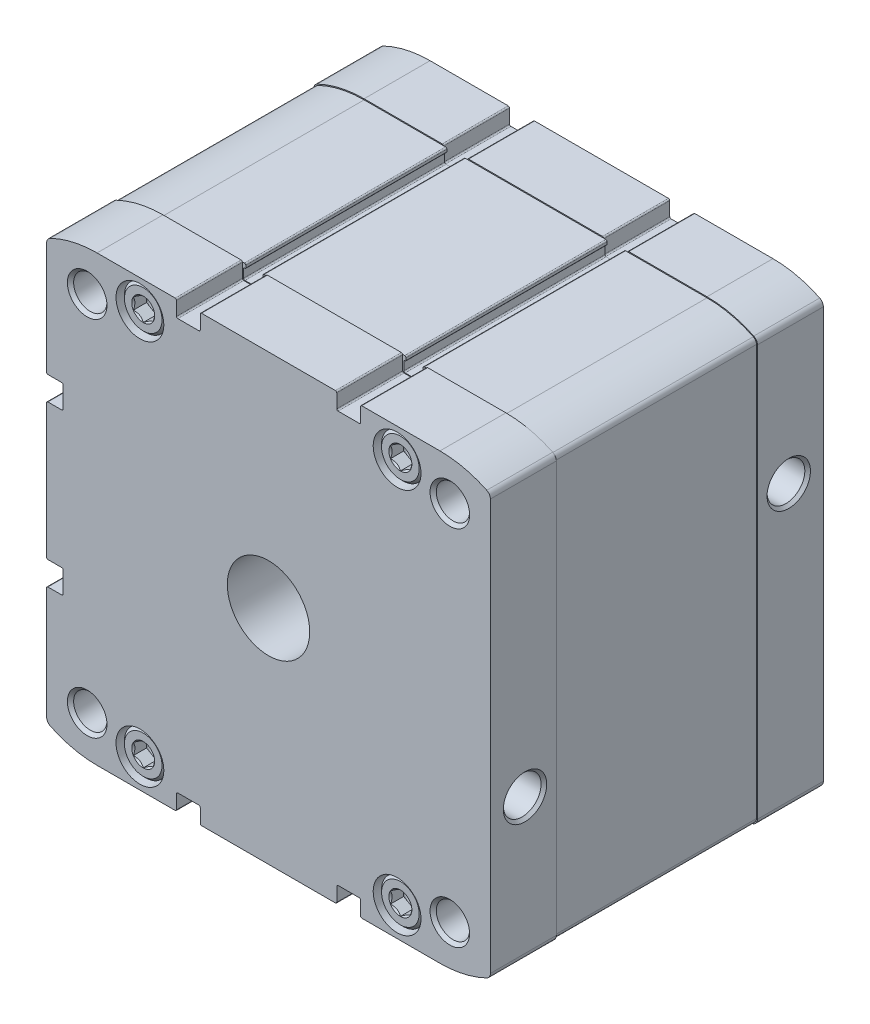
SolidWorks part; units mm, degrees
ref_plane "Front Plane" through (0, 0, 0) normal (0, 0, 1) x (1, 0, 0)
ref_plane "Top Plane" through (0, 0, 0) normal (0, 1, 0) x (1, 0, 0)
ref_plane "Right Plane" through (0, 0, 0) normal (1, 0, 0) x (0, 0, -1)
ref_plane "Plane1" through (0, 0, 0) normal (0, 0, 1) x (1, 0, 0)
sketch "Sketch1" plane through (0, 0, 0) normal (0, 0, 1) x (1, 0, 0)
  line L0 (-66.9, 27.9) -> (-62.7, 27.9)
  line L1 (-62.3, 27.5) -> (-62.3, 21.1)
  line L2 (-62.7, 20.7) -> (-66.9, 20.7)
  line L3 (-67.3, 20.3) -> (-67.3, -20.3)
  line L4 (-66.9, -20.7) -> (-62.7, -20.7)
  line L5 (-62.3, -21.1) -> (-62.3, -27.5)
  line L6 (-62.7, -27.9) -> (-66.9, -27.9)
  line L7 (-67.3, -28.3) -> (-67.3, -62.3009)
  line L8 (-52, -67.3) -> (-28.3, -67.3)
  line L9 (-27.9, -66.9) -> (-27.9, -62.7)
  line L10 (-27.5, -62.3) -> (-21.1, -62.3)
  line L11 (-20.7, -62.7) -> (-20.7, -66.9)
  line L12 (-20.3, -67.3) -> (20.3, -67.3)
  line L13 (20.7, -66.9) -> (20.7, -62.7)
  line L14 (21.1, -62.3) -> (27.5, -62.3)
  line L15 (27.9, -62.7) -> (27.9, -66.9)
  line L16 (28.3, -67.3) -> (52, -67.3)
  line L17 (67.3, -62.3009) -> (67.3, 62.3009)
  line L18 (52, 67.3) -> (28.3, 67.3)
  line L19 (27.9, 66.9) -> (27.9, 62.7)
  line L20 (27.5, 62.3) -> (21.1, 62.3)
  line L21 (20.7, 62.7) -> (20.7, 66.9)
  line L22 (20.3, 67.3) -> (-20.3, 67.3)
  line L23 (-20.7, 66.9) -> (-20.7, 62.7)
  line L24 (-21.1, 62.3) -> (-27.5, 62.3)
  line L25 (-27.9, 62.7) -> (-27.9, 66.9)
  line L26 (-28.3, 67.3) -> (-52, 67.3)
  line L27 (-67.3, 62.3009) -> (-67.3, 28.3)
  arc A0 (-67.3, 28.3) -> (-66.9, 27.9) centre (-66.9, 28.3) ccw
  arc A1 (-62.7, 27.9) -> (-62.3, 27.5) centre (-62.7, 27.5) cw
  arc A2 (-62.3, 21.1) -> (-62.7, 20.7) centre (-62.7, 21.1) cw
  arc A3 (-66.9, 20.7) -> (-67.3, 20.3) centre (-66.9, 20.3) ccw
  arc A4 (-67.3, -20.3) -> (-66.9, -20.7) centre (-66.9, -20.3) ccw
  arc A5 (-62.7, -20.7) -> (-62.3, -21.1) centre (-62.7, -21.1) cw
  arc A6 (-62.3, -27.5) -> (-62.7, -27.9) centre (-62.7, -27.5) cw
  arc A7 (-66.9, -27.9) -> (-67.3, -28.3) centre (-66.9, -28.3) ccw
  arc A8 (-67.3, -62.3009) -> (-66.1966, -64.0575) centre (-65.35, -62.3009) ccw
  arc A9 (-66.1966, -64.0575) -> (-52, -67.3) centre (-52, -34.6) ccw
  arc A10 (-28.3, -67.3) -> (-27.9, -66.9) centre (-28.3, -66.9) ccw
  arc A11 (-27.9, -62.7) -> (-27.5, -62.3) centre (-27.5, -62.7) cw
  arc A12 (-21.1, -62.3) -> (-20.7, -62.7) centre (-21.1, -62.7) cw
  arc A13 (-20.7, -66.9) -> (-20.3, -67.3) centre (-20.3, -66.9) ccw
  arc A14 (20.3, -67.3) -> (20.7, -66.9) centre (20.3, -66.9) ccw
  arc A15 (20.7, -62.7) -> (21.1, -62.3) centre (21.1, -62.7) cw
  arc A16 (27.5, -62.3) -> (27.9, -62.7) centre (27.5, -62.7) cw
  arc A17 (27.9, -66.9) -> (28.3, -67.3) centre (28.3, -66.9) ccw
  arc A18 (52, -67.3) -> (66.1966, -64.0575) centre (52, -34.6) ccw
  arc A19 (66.1966, -64.0575) -> (67.3, -62.3009) centre (65.35, -62.3009) ccw
  arc A20 (67.3, 62.3009) -> (66.1966, 64.0575) centre (65.35, 62.3009) ccw
  arc A21 (66.1966, 64.0575) -> (52, 67.3) centre (52, 34.6) ccw
  arc A22 (28.3, 67.3) -> (27.9, 66.9) centre (28.3, 66.9) ccw
  arc A23 (27.9, 62.7) -> (27.5, 62.3) centre (27.5, 62.7) cw
  arc A24 (21.1, 62.3) -> (20.7, 62.7) centre (21.1, 62.7) cw
  arc A25 (20.7, 66.9) -> (20.3, 67.3) centre (20.3, 66.9) ccw
  arc A26 (-20.3, 67.3) -> (-20.7, 66.9) centre (-20.3, 66.9) ccw
  arc A27 (-20.7, 62.7) -> (-21.1, 62.3) centre (-21.1, 62.7) cw
  arc A28 (-27.5, 62.3) -> (-27.9, 62.7) centre (-27.5, 62.7) cw
  arc A29 (-27.9, 66.9) -> (-28.3, 67.3) centre (-28.3, 66.9) ccw
  arc A30 (-52, 67.3) -> (-66.1966, 64.0575) centre (-52, 34.6) ccw
  arc A31 (-66.1966, 64.0575) -> (-67.3, 62.3009) centre (-65.35, 62.3009) ccw
extrude "Boss-Extrude1" add sketch "Sketch1" against normal blind 101
ref_plane "Plane2" through (0, 0, -20) normal (0, 0, 1) x (1, 0, 0)
sketch "Sketch2" plane through (0, 0, -20) normal (0, 0, 1) x (1, 0, 0)
  line L0 (-67, 67) -> (-67, -67)
  line L1 (-67, -67) -> (67, -67)
  line L2 (67, -67) -> (67, 67)
  line L3 (67, 67) -> (-67, 67)
extrude "Boss-Extrude2" add sketch "Sketch2" against normal blind 61
ref_plane "Plane3" through (0, 0, -20) normal (0, 0, 1) x (1, 0, 0)
sketch "Sketch3" plane through (0, 0, -20) normal (0, 0, 1) x (1, 0, 0)
  line L0 (-100, 100) -> (-100, -100)
  line L1 (-100, -100) -> (100, -100)
  line L2 (100, -100) -> (100, 100)
  line L3 (100, 100) -> (-100, 100)
  line L4 (-66.6, 26.9) -> (-65.9, 26.9)
  line L5 (-65.7, 27.1) -> (-65.7, 27.35)
  line L6 (-65.5, 27.55) -> (-62.9, 27.55)
  line L7 (-62.5, 27.15) -> (-62.5, 21.45)
  line L8 (-62.9, 21.05) -> (-65.5, 21.05)
  line L9 (-65.7, 21.25) -> (-65.7, 21.5)
  line L10 (-65.9, 21.7) -> (-66.6, 21.7)
  line L11 (-67, 21.3) -> (-67, -21.3)
  line L12 (-66.6, -21.7) -> (-65.9, -21.7)
  line L13 (-65.7, -21.5) -> (-65.7, -21.25)
  line L14 (-65.5, -21.05) -> (-62.9, -21.05)
  line L15 (-62.5, -21.45) -> (-62.5, -27.15)
  line L16 (-62.9, -27.55) -> (-65.5, -27.55)
  line L17 (-65.7, -27.35) -> (-65.7, -27.1)
  line L18 (-65.9, -26.9) -> (-66.6, -26.9)
  line L19 (-67, -27.3) -> (-67, -62.2695)
  line L20 (-52, -67) -> (-27.3, -67)
  line L21 (-26.9, -66.6) -> (-26.9, -65.9)
  line L22 (-27.1, -65.7) -> (-27.35, -65.7)
  line L23 (-27.55, -65.5) -> (-27.55, -62.9)
  line L24 (-27.15, -62.5) -> (-21.45, -62.5)
  line L25 (-21.05, -62.9) -> (-21.05, -65.5)
  line L26 (-21.25, -65.7) -> (-21.5, -65.7)
  line L27 (-21.7, -65.9) -> (-21.7, -66.6)
  line L28 (-21.3, -67) -> (21.3, -67)
  line L29 (21.7, -66.6) -> (21.7, -65.9)
  line L30 (21.5, -65.7) -> (21.25, -65.7)
  line L31 (21.05, -65.5) -> (21.05, -62.9)
  line L32 (21.45, -62.5) -> (27.15, -62.5)
  line L33 (27.55, -62.9) -> (27.55, -65.5)
  line L34 (27.35, -65.7) -> (27.1, -65.7)
  line L35 (26.9, -65.9) -> (26.9, -66.6)
  line L36 (27.3, -67) -> (52, -67)
  line L37 (67, -62.2695) -> (67, 62.2695)
  line L38 (52, 67) -> (27.3, 67)
  line L39 (26.9, 66.6) -> (26.9, 65.9)
  line L40 (27.1, 65.7) -> (27.35, 65.7)
  line L41 (27.55, 65.5) -> (27.55, 62.9)
  line L42 (27.15, 62.5) -> (21.45, 62.5)
  line L43 (21.05, 62.9) -> (21.05, 65.5)
  line L44 (21.25, 65.7) -> (21.5, 65.7)
  line L45 (21.7, 65.9) -> (21.7, 66.6)
  line L46 (21.3, 67) -> (-21.3, 67)
  line L47 (-21.7, 66.6) -> (-21.7, 65.9)
  line L48 (-21.5, 65.7) -> (-21.25, 65.7)
  line L49 (-21.05, 65.5) -> (-21.05, 62.9)
  line L50 (-21.45, 62.5) -> (-27.15, 62.5)
  line L51 (-27.55, 62.9) -> (-27.55, 65.5)
  line L52 (-27.35, 65.7) -> (-27.1, 65.7)
  line L53 (-26.9, 65.9) -> (-26.9, 66.6)
  line L54 (-27.3, 67) -> (-52, 67)
  line L55 (-67, 62.2695) -> (-67, 27.3)
  arc A0 (-67, 27.3) -> (-66.6, 26.9) centre (-66.6, 27.3) ccw
  arc A1 (-65.9, 26.9) -> (-65.7, 27.1) centre (-65.9, 27.1) ccw
  arc A2 (-65.7, 27.35) -> (-65.5, 27.55) centre (-65.5, 27.35) cw
  arc A3 (-62.9, 27.55) -> (-62.5, 27.15) centre (-62.9, 27.15) cw
  arc A4 (-62.5, 21.45) -> (-62.9, 21.05) centre (-62.9, 21.45) cw
  arc A5 (-65.5, 21.05) -> (-65.7, 21.25) centre (-65.5, 21.25) cw
  arc A6 (-65.7, 21.5) -> (-65.9, 21.7) centre (-65.9, 21.5) ccw
  arc A7 (-66.6, 21.7) -> (-67, 21.3) centre (-66.6, 21.3) ccw
  arc A8 (-67, -21.3) -> (-66.6, -21.7) centre (-66.6, -21.3) ccw
  arc A9 (-65.9, -21.7) -> (-65.7, -21.5) centre (-65.9, -21.5) ccw
  arc A10 (-65.7, -21.25) -> (-65.5, -21.05) centre (-65.5, -21.25) cw
  arc A11 (-62.9, -21.05) -> (-62.5, -21.45) centre (-62.9, -21.45) cw
  arc A12 (-62.5, -27.15) -> (-62.9, -27.55) centre (-62.9, -27.15) cw
  arc A13 (-65.5, -27.55) -> (-65.7, -27.35) centre (-65.5, -27.35) cw
  arc A14 (-65.7, -27.1) -> (-65.9, -26.9) centre (-65.9, -27.1) ccw
  arc A15 (-66.6, -26.9) -> (-67, -27.3) centre (-66.6, -27.3) ccw
  arc A16 (-67, -62.2695) -> (-66.0365, -63.8017) centre (-65.3, -62.2695) ccw
  arc A17 (-66.0365, -63.8017) -> (-52, -67) centre (-52, -34.6) ccw
  arc A18 (-27.3, -67) -> (-26.9, -66.6) centre (-27.3, -66.6) ccw
  arc A19 (-26.9, -65.9) -> (-27.1, -65.7) centre (-27.1, -65.9) ccw
  arc A20 (-27.35, -65.7) -> (-27.55, -65.5) centre (-27.35, -65.5) cw
  arc A21 (-27.55, -62.9) -> (-27.15, -62.5) centre (-27.15, -62.9) cw
  arc A22 (-21.45, -62.5) -> (-21.05, -62.9) centre (-21.45, -62.9) cw
  arc A23 (-21.05, -65.5) -> (-21.25, -65.7) centre (-21.25, -65.5) cw
  arc A24 (-21.5, -65.7) -> (-21.7, -65.9) centre (-21.5, -65.9) ccw
  arc A25 (-21.7, -66.6) -> (-21.3, -67) centre (-21.3, -66.6) ccw
  arc A26 (21.3, -67) -> (21.7, -66.6) centre (21.3, -66.6) ccw
  arc A27 (21.7, -65.9) -> (21.5, -65.7) centre (21.5, -65.9) ccw
  arc A28 (21.25, -65.7) -> (21.05, -65.5) centre (21.25, -65.5) cw
  arc A29 (21.05, -62.9) -> (21.45, -62.5) centre (21.45, -62.9) cw
  arc A30 (27.15, -62.5) -> (27.55, -62.9) centre (27.15, -62.9) cw
  arc A31 (27.55, -65.5) -> (27.35, -65.7) centre (27.35, -65.5) cw
  arc A32 (27.1, -65.7) -> (26.9, -65.9) centre (27.1, -65.9) ccw
  arc A33 (26.9, -66.6) -> (27.3, -67) centre (27.3, -66.6) ccw
  arc A34 (52, -67) -> (66.0365, -63.8017) centre (52, -34.6) ccw
  arc A35 (66.0365, -63.8017) -> (67, -62.2695) centre (65.3, -62.2695) ccw
  arc A36 (67, 62.2695) -> (66.0365, 63.8017) centre (65.3, 62.2695) ccw
  arc A37 (66.0365, 63.8017) -> (52, 67) centre (52, 34.6) ccw
  arc A38 (27.3, 67) -> (26.9, 66.6) centre (27.3, 66.6) ccw
  arc A39 (26.9, 65.9) -> (27.1, 65.7) centre (27.1, 65.9) ccw
  arc A40 (27.35, 65.7) -> (27.55, 65.5) centre (27.35, 65.5) cw
  arc A41 (27.55, 62.9) -> (27.15, 62.5) centre (27.15, 62.9) cw
  arc A42 (21.45, 62.5) -> (21.05, 62.9) centre (21.45, 62.9) cw
  arc A43 (21.05, 65.5) -> (21.25, 65.7) centre (21.25, 65.5) cw
  arc A44 (21.5, 65.7) -> (21.7, 65.9) centre (21.5, 65.9) ccw
  arc A45 (21.7, 66.6) -> (21.3, 67) centre (21.3, 66.6) ccw
  arc A46 (-21.3, 67) -> (-21.7, 66.6) centre (-21.3, 66.6) ccw
  arc A47 (-21.7, 65.9) -> (-21.5, 65.7) centre (-21.5, 65.9) ccw
  arc A48 (-21.25, 65.7) -> (-21.05, 65.5) centre (-21.25, 65.5) cw
  arc A49 (-21.05, 62.9) -> (-21.45, 62.5) centre (-21.45, 62.9) cw
  arc A50 (-27.15, 62.5) -> (-27.55, 62.9) centre (-27.15, 62.9) cw
  arc A51 (-27.55, 65.5) -> (-27.35, 65.7) centre (-27.35, 65.5) cw
  arc A52 (-27.1, 65.7) -> (-26.9, 65.9) centre (-27.1, 65.9) ccw
  arc A53 (-26.9, 66.6) -> (-27.3, 67) centre (-27.3, 66.6) ccw
  arc A54 (-52, 67) -> (-66.0365, 63.8017) centre (-52, 34.6) ccw
  arc A55 (-66.0365, 63.8017) -> (-67, 62.2695) centre (-65.3, 62.2695) ccw
extrude "Cut-Extrude1" cut sketch "Sketch3" against normal blind 61
ref_plane "Plane4" through (0, -21.15, 0) normal (0, 1, 0) x (1, 0, 0)
sketch "Sketch4" plane through (0, -21.15, 0) normal (0, 1, 0) x (1, 0, 0)
  line L0 (39.5, 10.5) -> (39.5, 16.2225)
  line L1 (39.5, 16.2225) -> (66.444, 16.2225)
  line L2 (66.444, 16.2225) -> (67.3, 17.0785)
  line L3 (67.3, 17.0785) -> (67.3, 10.5)
  line L4 (67.3, 10.5) -> (39.5, 10.5)
  line L5 (67.3, 10.5) -> (39.5, 10.5) construction
revolve "Cut-Revolve1" cut sketch "Sketch4" angle 360 about L5
cosmetic thread "Cosmetic Thread1" parameters "D1"=13, "D2"=13.157
ref_plane "Plane5" through (0, 21.15, 0) normal (0, 1, 0) x (1, 0, 0)
sketch "Sketch5" plane through (0, 21.15, 0) normal (0, 1, 0) x (1, 0, 0)
  line L0 (39.5, 90.5) -> (39.5, 96.2225)
  line L1 (39.5, 96.2225) -> (66.444, 96.2225)
  line L2 (66.444, 96.2225) -> (67.3, 97.0785)
  line L3 (67.3, 97.0785) -> (67.3, 90.5)
  line L4 (67.3, 90.5) -> (39.5, 90.5)
  line L5 (67.3, 90.5) -> (39.5, 90.5) construction
revolve "Cut-Revolve2" cut sketch "Sketch5" angle 360 about L5
cosmetic thread "Cosmetic Thread2" parameters "D1"=13, "D2"=13.157
ref_plane "Plane6" through (0, 0, 0) normal (1, 0, 0) x (0, 0, -1)
sketch "Sketch6" plane through (0, 0, 0) normal (1, 0, 0) x (0, 0, -1)
  line L0 (-1, 0) -> (-1, 12.5)
  line L1 (-1, 12.5) -> (28.75, 12.5)
  line L2 (28.75, 12.5) -> (28.75, 62.5)
  line L3 (28.75, 62.5) -> (80, 62.5)
  line L4 (80, 62.5) -> (80, 0)
  line L5 (80, 0) -> (-1, 0)
  line L6 (80, 0) -> (-1, 0) construction
revolve "Cut-Revolve3" cut sketch "Sketch6" angle 360 about L6
ref_plane "Plane7" through (0, 0, 0) normal (1, 0, 0) x (0, 0, -1)
sketch "Sketch7" plane through (0, 0, 0) normal (1, 0, 0) x (0, 0, -1)
  line L0 (98.4, 0) -> (98.4, 6)
  line L1 (98.4, 6) -> (101, 6)
  line L2 (101, 6) -> (101, 0)
  line L3 (101, 0) -> (98.4, 0)
  line L4 (101, 0) -> (98.4, 0) construction
revolve "Cut-Revolve4" cut sketch "Sketch7" angle 360 about L4
ref_plane "Plane8" through (0, 58.5, 0) normal (0, 1, 0) x (1, 0, 0)
sketch "Sketch8" plane through (0, 58.5, 0) normal (0, 1, 0) x (1, 0, 0)
  line L0 (39, 5.8038) -> (42, 5)
  line L1 (42, 5) -> (42, 1.48)
  line L2 (42, 1.48) -> (42.48, 1)
  line L3 (42.48, 1) -> (44.7, 1)
  line L4 (44.7, 1) -> (45.5, 1.8)
  line L5 (45.5, 1.8) -> (45.5, 9)
  line L6 (45.5, 9) -> (46.25, 9)
  line L7 (46.25, 9) -> (46.25, -1)
  line L8 (46.25, -1) -> (39, -1)
  line L9 (39, -1) -> (39, 5.8038)
  line L10 (39, -1) -> (39, 5.8038) construction
revolve "Cut-Revolve5" cut sketch "Sketch8" angle 360 about L10
ref_plane "Plane9" through (0, 58.5, 0) normal (0, 1, 0) x (1, 0, 0)
sketch "Sketch9" plane through (0, 58.5, 0) normal (0, 1, 0) x (1, 0, 0)
  line L0 (-39, 5.8038) -> (-36, 5)
  line L1 (-36, 5) -> (-36, 1.48)
  line L2 (-36, 1.48) -> (-35.52, 1)
  line L3 (-35.52, 1) -> (-33.3, 1)
  line L4 (-33.3, 1) -> (-32.5, 1.8)
  line L5 (-32.5, 1.8) -> (-32.5, 9)
  line L6 (-32.5, 9) -> (-31.75, 9)
  line L7 (-31.75, 9) -> (-31.75, -1)
  line L8 (-31.75, -1) -> (-39, -1)
  line L9 (-39, -1) -> (-39, 5.8038)
  line L10 (-39, -1) -> (-39, 5.8038) construction
revolve "Cut-Revolve6" cut sketch "Sketch9" angle 360 about L10
ref_plane "Plane10" through (0, -58.5, 0) normal (0, 1, 0) x (1, 0, 0)
sketch "Sketch10" plane through (0, -58.5, 0) normal (0, 1, 0) x (1, 0, 0)
  line L0 (39, 5.8038) -> (42, 5)
  line L1 (42, 5) -> (42, 1.48)
  line L2 (42, 1.48) -> (42.48, 1)
  line L3 (42.48, 1) -> (44.7, 1)
  line L4 (44.7, 1) -> (45.5, 1.8)
  line L5 (45.5, 1.8) -> (45.5, 9)
  line L6 (45.5, 9) -> (46.25, 9)
  line L7 (46.25, 9) -> (46.25, -1)
  line L8 (46.25, -1) -> (39, -1)
  line L9 (39, -1) -> (39, 5.8038)
  line L10 (39, -1) -> (39, 5.8038) construction
revolve "Cut-Revolve7" cut sketch "Sketch10" angle 360 about L10
ref_plane "Plane11" through (0, -58.5, 0) normal (0, 1, 0) x (1, 0, 0)
sketch "Sketch11" plane through (0, -58.5, 0) normal (0, 1, 0) x (1, 0, 0)
  line L0 (-39, 5.8038) -> (-36, 5)
  line L1 (-36, 5) -> (-36, 1.48)
  line L2 (-36, 1.48) -> (-35.52, 1)
  line L3 (-35.52, 1) -> (-33.3, 1)
  line L4 (-33.3, 1) -> (-32.5, 1.8)
  line L5 (-32.5, 1.8) -> (-32.5, 9)
  line L6 (-32.5, 9) -> (-31.75, 9)
  line L7 (-31.75, 9) -> (-31.75, -1)
  line L8 (-31.75, -1) -> (-39, -1)
  line L9 (-39, -1) -> (-39, 5.8038)
  line L10 (-39, -1) -> (-39, 5.8038) construction
revolve "Cut-Revolve8" cut sketch "Sketch11" angle 360 about L10
ref_plane "Plane12" through (0, 58.5, 0) normal (0, 1, 0) x (1, 0, 0)
sketch "Sketch12" plane through (0, 58.5, 0) normal (0, 1, 0) x (1, 0, 0)
  line L0 (39, 102) -> (46.25, 102)
  line L1 (46.25, 102) -> (46.25, 92)
  line L2 (46.25, 92) -> (45.5, 92)
  line L3 (45.5, 92) -> (45.5, 99.2)
  line L4 (45.5, 99.2) -> (44.7, 100)
  line L5 (44.7, 100) -> (42.48, 100)
  line L6 (42.48, 100) -> (42, 99.52)
  line L7 (42, 99.52) -> (42, 96)
  line L8 (42, 96) -> (39, 95.1962)
  line L9 (39, 95.1962) -> (39, 102)
  line L10 (39, 95.1962) -> (39, 102) construction
revolve "Cut-Revolve9" cut sketch "Sketch12" angle 360 about L10
ref_plane "Plane13" through (0, 58.5, 0) normal (0, 1, 0) x (1, 0, 0)
sketch "Sketch13" plane through (0, 58.5, 0) normal (0, 1, 0) x (1, 0, 0)
  line L0 (-39, 102) -> (-31.75, 102)
  line L1 (-31.75, 102) -> (-31.75, 92)
  line L2 (-31.75, 92) -> (-32.5, 92)
  line L3 (-32.5, 92) -> (-32.5, 99.2)
  line L4 (-32.5, 99.2) -> (-33.3, 100)
  line L5 (-33.3, 100) -> (-35.52, 100)
  line L6 (-35.52, 100) -> (-36, 99.52)
  line L7 (-36, 99.52) -> (-36, 96)
  line L8 (-36, 96) -> (-39, 95.1962)
  line L9 (-39, 95.1962) -> (-39, 102)
  line L10 (-39, 95.1962) -> (-39, 102) construction
revolve "Cut-Revolve10" cut sketch "Sketch13" angle 360 about L10
ref_plane "Plane14" through (0, -58.5, 0) normal (0, 1, 0) x (1, 0, 0)
sketch "Sketch14" plane through (0, -58.5, 0) normal (0, 1, 0) x (1, 0, 0)
  line L0 (-39, 102) -> (-31.75, 102)
  line L1 (-31.75, 102) -> (-31.75, 92)
  line L2 (-31.75, 92) -> (-32.5, 92)
  line L3 (-32.5, 92) -> (-32.5, 99.2)
  line L4 (-32.5, 99.2) -> (-33.3, 100)
  line L5 (-33.3, 100) -> (-35.52, 100)
  line L6 (-35.52, 100) -> (-36, 99.52)
  line L7 (-36, 99.52) -> (-36, 96)
  line L8 (-36, 96) -> (-39, 95.1962)
  line L9 (-39, 95.1962) -> (-39, 102)
  line L10 (-39, 95.1962) -> (-39, 102) construction
revolve "Cut-Revolve11" cut sketch "Sketch14" angle 360 about L10
ref_plane "Plane15" through (0, -58.5, 0) normal (0, 1, 0) x (1, 0, 0)
sketch "Sketch15" plane through (0, -58.5, 0) normal (0, 1, 0) x (1, 0, 0)
  line L0 (39, 102) -> (46.25, 102)
  line L1 (46.25, 102) -> (46.25, 92)
  line L2 (46.25, 92) -> (45.5, 92)
  line L3 (45.5, 92) -> (45.5, 99.2)
  line L4 (45.5, 99.2) -> (44.7, 100)
  line L5 (44.7, 100) -> (42.48, 100)
  line L6 (42.48, 100) -> (42, 99.52)
  line L7 (42, 99.52) -> (42, 96)
  line L8 (42, 96) -> (39, 95.1962)
  line L9 (39, 95.1962) -> (39, 102)
  line L10 (39, 95.1962) -> (39, 102) construction
revolve "Cut-Revolve12" cut sketch "Sketch15" angle 360 about L10
ref_plane "Plane16" through (0, 0, -1) normal (0, 0, 1) x (1, 0, 0)
sketch "Sketch16" plane through (0, 0, -1) normal (0, 0, 1) x (1, 0, 0)
  line L0 (36, 56.7679) -> (39, 55.0359)
  line L1 (39, 55.0359) -> (42, 56.7679)
  line L2 (42, 56.7679) -> (42, 60.2321)
  line L3 (42, 60.2321) -> (39, 61.9641)
  line L4 (39, 61.9641) -> (36, 60.2321)
  line L5 (36, 60.2321) -> (36, 56.7679)
extrude "Cut-Extrude2" cut sketch "Sketch16" against normal blind 4
ref_plane "Plane17" through (0, 0, -1) normal (0, 0, 1) x (1, 0, 0)
sketch "Sketch17" plane through (0, 0, -1) normal (0, 0, 1) x (1, 0, 0)
  line L0 (-42, 56.7679) -> (-39, 55.0359)
  line L1 (-39, 55.0359) -> (-36, 56.7679)
  line L2 (-36, 56.7679) -> (-36, 60.2321)
  line L3 (-36, 60.2321) -> (-39, 61.9641)
  line L4 (-39, 61.9641) -> (-42, 60.2321)
  line L5 (-42, 60.2321) -> (-42, 56.7679)
extrude "Cut-Extrude3" cut sketch "Sketch17" against normal blind 4
ref_plane "Plane18" through (0, 0, -1) normal (0, 0, 1) x (1, 0, 0)
sketch "Sketch18" plane through (0, 0, -1) normal (0, 0, 1) x (1, 0, 0)
  line L0 (-42, -60.2321) -> (-39, -61.9641)
  line L1 (-39, -61.9641) -> (-36, -60.2321)
  line L2 (-36, -60.2321) -> (-36, -56.7679)
  line L3 (-36, -56.7679) -> (-39, -55.0359)
  line L4 (-39, -55.0359) -> (-42, -56.7679)
  line L5 (-42, -56.7679) -> (-42, -60.2321)
extrude "Cut-Extrude4" cut sketch "Sketch18" against normal blind 4
ref_plane "Plane19" through (0, 0, -1) normal (0, 0, 1) x (1, 0, 0)
sketch "Sketch19" plane through (0, 0, -1) normal (0, 0, 1) x (1, 0, 0)
  line L0 (36, -60.2321) -> (39, -61.9641)
  line L1 (39, -61.9641) -> (42, -60.2321)
  line L2 (42, -60.2321) -> (42, -56.7679)
  line L3 (42, -56.7679) -> (39, -55.0359)
  line L4 (39, -55.0359) -> (36, -56.7679)
  line L5 (36, -56.7679) -> (36, -60.2321)
extrude "Cut-Extrude5" cut sketch "Sketch19" against normal blind 4
ref_plane "Plane20" through (0, 0, -100) normal (0, 0, 1) x (1, 0, 0)
sketch "Sketch20" plane through (0, 0, -100) normal (0, 0, 1) x (1, 0, 0)
  line L0 (36, 56.7679) -> (39, 55.0359)
  line L1 (39, 55.0359) -> (42, 56.7679)
  line L2 (42, 56.7679) -> (42, 60.2321)
  line L3 (42, 60.2321) -> (39, 61.9641)
  line L4 (39, 61.9641) -> (36, 60.2321)
  line L5 (36, 60.2321) -> (36, 56.7679)
extrude "Cut-Extrude6" cut sketch "Sketch20" along normal blind 4
ref_plane "Plane21" through (0, 0, -100) normal (0, 0, 1) x (1, 0, 0)
sketch "Sketch21" plane through (0, 0, -100) normal (0, 0, 1) x (1, 0, 0)
  line L0 (-42, 56.7679) -> (-39, 55.0359)
  line L1 (-39, 55.0359) -> (-36, 56.7679)
  line L2 (-36, 56.7679) -> (-36, 60.2321)
  line L3 (-36, 60.2321) -> (-39, 61.9641)
  line L4 (-39, 61.9641) -> (-42, 60.2321)
  line L5 (-42, 60.2321) -> (-42, 56.7679)
extrude "Cut-Extrude7" cut sketch "Sketch21" along normal blind 4
ref_plane "Plane22" through (0, 0, -100) normal (0, 0, 1) x (1, 0, 0)
sketch "Sketch22" plane through (0, 0, -100) normal (0, 0, 1) x (1, 0, 0)
  line L0 (-42, -60.2321) -> (-39, -61.9641)
  line L1 (-39, -61.9641) -> (-36, -60.2321)
  line L2 (-36, -60.2321) -> (-36, -56.7679)
  line L3 (-36, -56.7679) -> (-39, -55.0359)
  line L4 (-39, -55.0359) -> (-42, -56.7679)
  line L5 (-42, -56.7679) -> (-42, -60.2321)
extrude "Cut-Extrude8" cut sketch "Sketch22" along normal blind 4
ref_plane "Plane23" through (0, 0, -100) normal (0, 0, 1) x (1, 0, 0)
sketch "Sketch23" plane through (0, 0, -100) normal (0, 0, 1) x (1, 0, 0)
  line L0 (36, -60.2321) -> (39, -61.9641)
  line L1 (39, -61.9641) -> (42, -60.2321)
  line L2 (42, -60.2321) -> (42, -56.7679)
  line L3 (42, -56.7679) -> (39, -55.0359)
  line L4 (39, -55.0359) -> (36, -56.7679)
  line L5 (36, -56.7679) -> (36, -60.2321)
extrude "Cut-Extrude9" cut sketch "Sketch23" along normal blind 4
ref_plane "Plane24" through (55, 0, 0) normal (1, 0, 0) x (0, 0, -1)
sketch "Sketch24" plane through (55, 0, 0) normal (1, 0, 0) x (0, 0, -1)
  line L0 (0, 55) -> (0, 61)
  line L1 (0, 61) -> (0.947, 60.053)
  line L2 (0.947, 60.053) -> (20, 60.053)
  line L3 (20, 60.053) -> (20, 55)
  line L4 (20, 55) -> (0, 55)
  line L5 (20, 55) -> (0, 55) construction
revolve "Cut-Revolve13" cut sketch "Sketch24" angle 360 about L5
cosmetic thread "Cosmetic Thread3" parameters "D1"=20, "D2"=12
ref_plane "Plane25" through (-55, 0, 0) normal (1, 0, 0) x (0, 0, -1)
sketch "Sketch25" plane through (-55, 0, 0) normal (1, 0, 0) x (0, 0, -1)
  line L0 (0, 55) -> (0, 61)
  line L1 (0, 61) -> (0.947, 60.053)
  line L2 (0.947, 60.053) -> (20, 60.053)
  line L3 (20, 60.053) -> (20, 55)
  line L4 (20, 55) -> (0, 55)
  line L5 (20, 55) -> (0, 55) construction
revolve "Cut-Revolve14" cut sketch "Sketch25" angle 360 about L5
cosmetic thread "Cosmetic Thread4" parameters "D1"=20, "D2"=12
ref_plane "Plane26" through (55, 0, 0) normal (1, 0, 0) x (0, 0, -1)
sketch "Sketch26" plane through (55, 0, 0) normal (1, 0, 0) x (0, 0, -1)
  line L0 (0, -55) -> (0, -49)
  line L1 (0, -49) -> (0.947, -49.947)
  line L2 (0.947, -49.947) -> (20, -49.947)
  line L3 (20, -49.947) -> (20, -55)
  line L4 (20, -55) -> (0, -55)
  line L5 (20, -55) -> (0, -55) construction
revolve "Cut-Revolve15" cut sketch "Sketch26" angle 360 about L5
cosmetic thread "Cosmetic Thread5" parameters "D1"=20, "D2"=12
ref_plane "Plane27" through (-55, 0, 0) normal (1, 0, 0) x (0, 0, -1)
sketch "Sketch27" plane through (-55, 0, 0) normal (1, 0, 0) x (0, 0, -1)
  line L0 (0, -55) -> (0, -49)
  line L1 (0, -49) -> (0.947, -49.947)
  line L2 (0.947, -49.947) -> (20, -49.947)
  line L3 (20, -49.947) -> (20, -55)
  line L4 (20, -55) -> (0, -55)
  line L5 (20, -55) -> (0, -55) construction
revolve "Cut-Revolve16" cut sketch "Sketch27" angle 360 about L5
cosmetic thread "Cosmetic Thread6" parameters "D1"=20, "D2"=12
ref_plane "Plane28" through (55, 0, 0) normal (1, 0, 0) x (0, 0, -1)
sketch "Sketch28" plane through (55, 0, 0) normal (1, 0, 0) x (0, 0, -1)
  line L0 (81, 55) -> (81, 60.053)
  line L1 (81, 60.053) -> (100.053, 60.053)
  line L2 (100.053, 60.053) -> (101, 61)
  line L3 (101, 61) -> (101, 55)
  line L4 (101, 55) -> (81, 55)
  line L5 (101, 55) -> (81, 55) construction
revolve "Cut-Revolve17" cut sketch "Sketch28" angle 360 about L5
cosmetic thread "Cosmetic Thread7" parameters "D1"=20, "D2"=12
ref_plane "Plane29" through (55, 0, 0) normal (1, 0, 0) x (0, 0, -1)
sketch "Sketch29" plane through (55, 0, 0) normal (1, 0, 0) x (0, 0, -1)
  line L0 (20, 55) -> (20, 60.5)
  line L1 (20, 60.5) -> (81, 60.5)
  line L2 (81, 60.5) -> (81, 55)
  line L3 (81, 55) -> (20, 55)
  line L4 (81, 55) -> (20, 55) construction
revolve "Cut-Revolve18" cut sketch "Sketch29" angle 360 about L4
ref_plane "Plane30" through (-55, 0, 0) normal (1, 0, 0) x (0, 0, -1)
sketch "Sketch30" plane through (-55, 0, 0) normal (1, 0, 0) x (0, 0, -1)
  line L0 (81, 55) -> (81, 60.053)
  line L1 (81, 60.053) -> (100.053, 60.053)
  line L2 (100.053, 60.053) -> (101, 61)
  line L3 (101, 61) -> (101, 55)
  line L4 (101, 55) -> (81, 55)
  line L5 (101, 55) -> (81, 55) construction
revolve "Cut-Revolve19" cut sketch "Sketch30" angle 360 about L5
cosmetic thread "Cosmetic Thread8" parameters "D1"=20, "D2"=12
ref_plane "Plane31" through (-55, 0, 0) normal (1, 0, 0) x (0, 0, -1)
sketch "Sketch31" plane through (-55, 0, 0) normal (1, 0, 0) x (0, 0, -1)
  line L0 (20, 55) -> (20, 60.5)
  line L1 (20, 60.5) -> (81, 60.5)
  line L2 (81, 60.5) -> (81, 55)
  line L3 (81, 55) -> (20, 55)
  line L4 (81, 55) -> (20, 55) construction
revolve "Cut-Revolve20" cut sketch "Sketch31" angle 360 about L4
ref_plane "Plane32" through (55, 0, 0) normal (1, 0, 0) x (0, 0, -1)
sketch "Sketch32" plane through (55, 0, 0) normal (1, 0, 0) x (0, 0, -1)
  line L0 (81, -55) -> (81, -49.947)
  line L1 (81, -49.947) -> (100.053, -49.947)
  line L2 (100.053, -49.947) -> (101, -49)
  line L3 (101, -49) -> (101, -55)
  line L4 (101, -55) -> (81, -55)
  line L5 (101, -55) -> (81, -55) construction
revolve "Cut-Revolve21" cut sketch "Sketch32" angle 360 about L5
cosmetic thread "Cosmetic Thread9" parameters "D1"=20, "D2"=12
ref_plane "Plane33" through (55, 0, 0) normal (1, 0, 0) x (0, 0, -1)
sketch "Sketch33" plane through (55, 0, 0) normal (1, 0, 0) x (0, 0, -1)
  line L0 (20, -55) -> (20, -49.5)
  line L1 (20, -49.5) -> (81, -49.5)
  line L2 (81, -49.5) -> (81, -55)
  line L3 (81, -55) -> (20, -55)
  line L4 (81, -55) -> (20, -55) construction
revolve "Cut-Revolve22" cut sketch "Sketch33" angle 360 about L4
ref_plane "Plane34" through (-55, 0, 0) normal (1, 0, 0) x (0, 0, -1)
sketch "Sketch34" plane through (-55, 0, 0) normal (1, 0, 0) x (0, 0, -1)
  line L0 (81, -55) -> (81, -49.947)
  line L1 (81, -49.947) -> (100.053, -49.947)
  line L2 (100.053, -49.947) -> (101, -49)
  line L3 (101, -49) -> (101, -55)
  line L4 (101, -55) -> (81, -55)
  line L5 (101, -55) -> (81, -55) construction
revolve "Cut-Revolve23" cut sketch "Sketch34" angle 360 about L5
cosmetic thread "Cosmetic Thread10" parameters "D1"=20, "D2"=12
ref_plane "Plane35" through (-55, 0, 0) normal (1, 0, 0) x (0, 0, -1)
sketch "Sketch35" plane through (-55, 0, 0) normal (1, 0, 0) x (0, 0, -1)
  line L0 (20, -55) -> (20, -49.5)
  line L1 (20, -49.5) -> (81, -49.5)
  line L2 (81, -49.5) -> (81, -55)
  line L3 (81, -55) -> (20, -55)
  line L4 (81, -55) -> (20, -55) construction
revolve "Cut-Revolve24" cut sketch "Sketch35" angle 360 about L4
